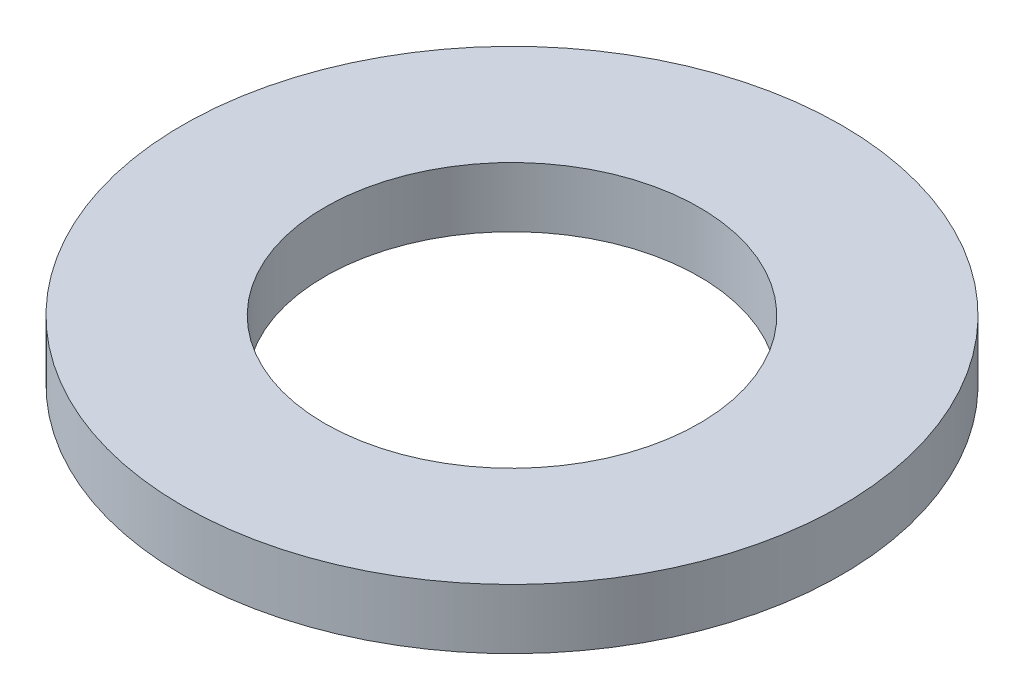
SolidWorks part; units mm, degrees
material "1023 Carbon Steel Sheet (SS)"
ref_plane "Front Plane" through (0, 0, 0) normal (0, 0, 1) x (1, 0, 0)
ref_plane "Top Plane" through (0, 0, 0) normal (0, 1, 0) x (1, 0, 0)
ref_plane "Right Plane" through (0, 0, 0) normal (1, 0, 0) x (0, 0, -1)
sketch "Sketch1" plane through (0, 0, 0) normal (0, 1, 0) x (1, 0, 0)
  circle A0 centre (0, 0) radius 12.5
  circle A1 centre (0, 0) radius 22
  dimension "D1" = 44
  dimension "D2" = 25
extrude "Boss-Extrude1" add sketch "Sketch1" along normal blind 4
